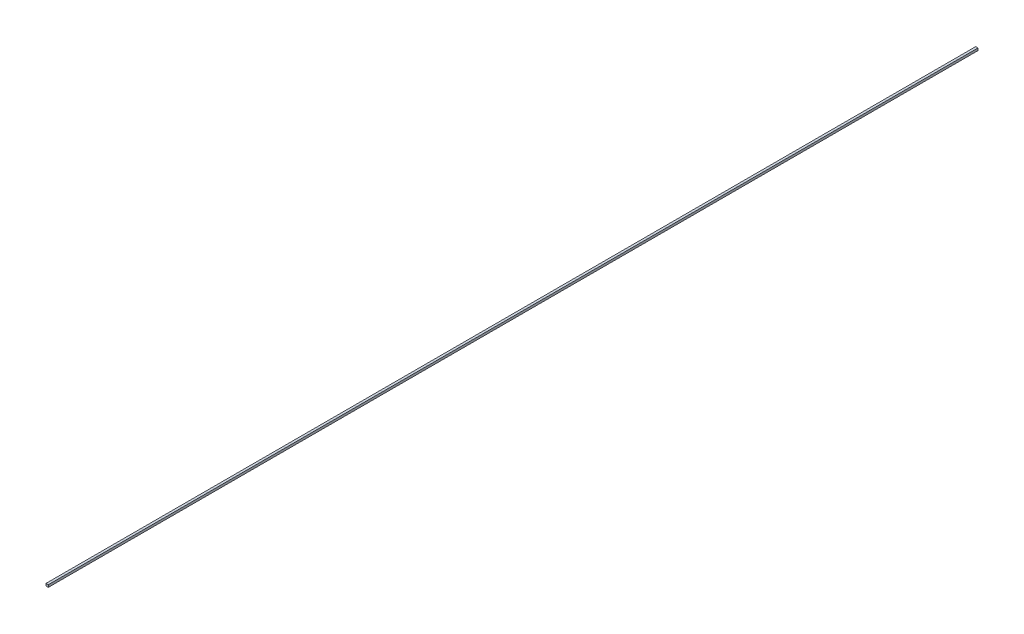
SolidWorks part; units mm, degrees
material "Balsa"
ref_plane "Front Plane" through (0, 0, 0) normal (0, 0, 1) x (1, 0, 0)
ref_plane "Top Plane" through (0, 0, 0) normal (0, 1, 0) x (1, 0, 0)
ref_plane "Right Plane" through (0, 0, 0) normal (1, 0, 0) x (0, 0, -1)
sketch "Sketch1" plane through (0, 0, 0) normal (0, 0, 1) x (1, 0, 0)
  line L1 (-1.5, 1.5) -> (1.5, 1.5)
  line L2 (-1.5, 1.5) -> (-1.5, -1.5)
  line L3 (-1.5, -1.5) -> (1.5, -1.5)
  line L4 (1.5, 1.5) -> (1.5, -1.5)
  line L5 (-1.5, 1.5) -> (1.5, -1.5) construction
  line L6 (-1.5, -1.5) -> (1.5, 1.5) construction
  point P0 (0, 0)
  dimension "D1" = 3
  dimension "D2" = 3
extrude "Boss-Extrude1" add sketch "Sketch1" along normal blind 1200
